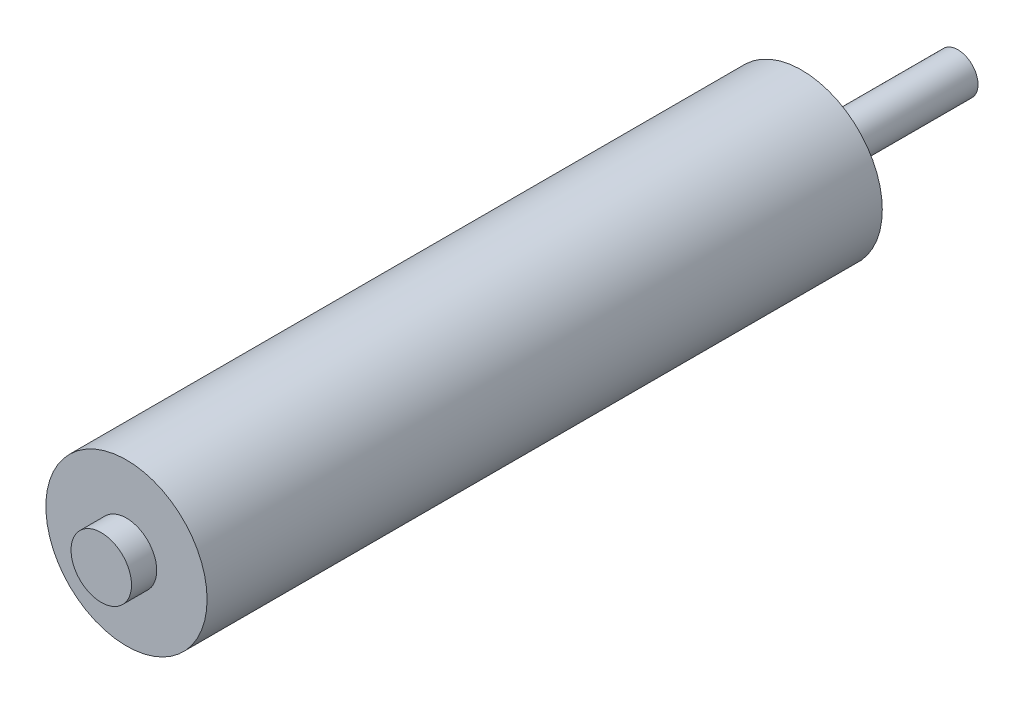
SolidWorks part; units mm, degrees
ref_plane "Front Plane" through (0, 0, 0) normal (0, 0, 1) x (1, 0, 0)
ref_plane "Top Plane" through (0, 0, 0) normal (0, 1, 0) x (1, 0, 0)
ref_plane "Right Plane" through (0, 0, 0) normal (1, 0, 0) x (0, 0, -1)
sketch "Sketch1" plane through (0, 0, 0) normal (0, 0, 1) x (1, 0, 0)
  circle A0 centre (0, 0) radius 8
extrude "Boss-Extrude1" add sketch "Sketch1" along normal blind 67
sketch "Sketch2" plane through (0, 0, 67) normal (0, 0, 1) x (1, 0, 0)
  circle A0 centre (0, 0) radius 3
extrude "Boss-Extrude2" add sketch "Sketch2" along normal blind 2.5
sketch "Sketch3" plane through (0, 0, 0) normal (0, 0, -1) x (-1, 0, 0)
  circle A0 centre (0, 0) radius 3
extrude "Boss-Extrude3" add sketch "Sketch3" along normal blind 2.5
sketch "Sketch4" plane through (0, 0, -2.5) normal (0, 0, -1) x (-1, 0, 0)
  circle A0 centre (0, 0) radius 2
extrude "Boss-Extrude4" add sketch "Sketch4" along normal blind 13
